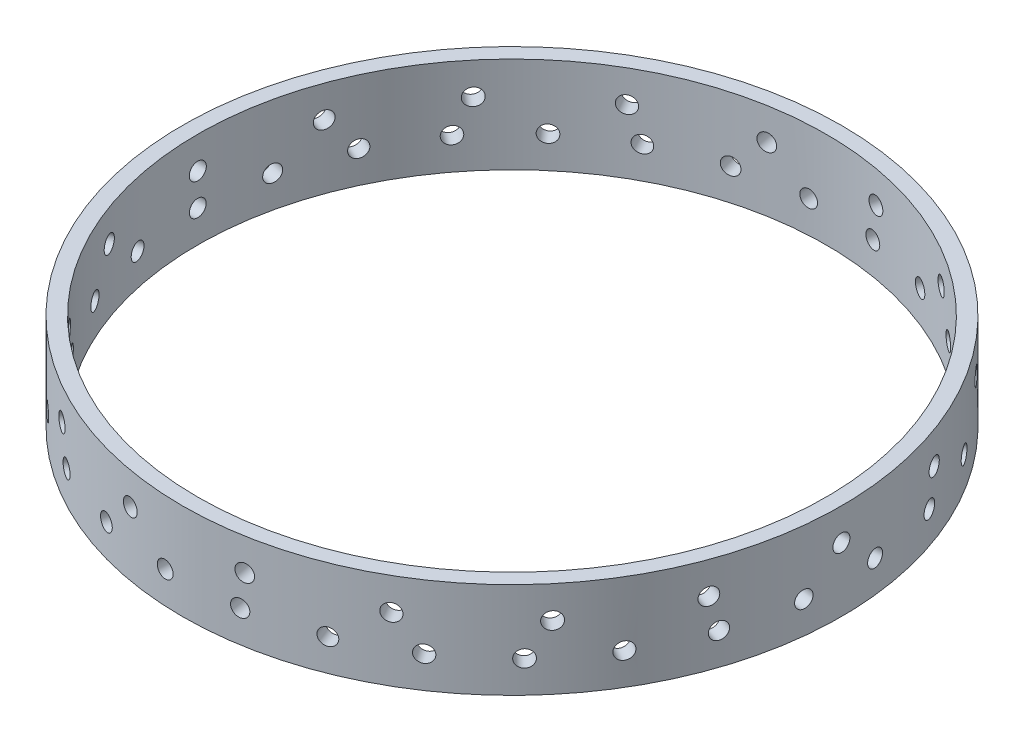
SolidWorks part; units mm, degrees
ref_plane "Front Plane" through (0, 0, 0) normal (0, 0, 1) x (1, 0, 0)
ref_plane "Top Plane" through (0, 0, 0) normal (0, 1, 0) x (1, 0, 0)
ref_plane "Right Plane" through (0, 0, 0) normal (1, 0, 0) x (0, 0, -1)
sketch "Sketch3" plane through (0, 0, 0) normal (1, 0, 0) x (0, 0, -1)
  line L0 (0, 0) -> (0, 34.4201) construction
  point P3 (0, 34.4201)
sketch "Sketch1" plane through (0, 0, 0) normal (0, 1, 0) x (1, 0, 0)
  circle A0 centre (0, 0) radius 68.58
  circle A1 centre (0, 0) radius 65.405
  dimension "D1" = 130.81
  dimension "D2" = 137.16
extrude "Boss-Extrude1" add sketch "Sketch1" along normal blind 19.9644
sketch "Sketch2" plane through (0, 0, 0) normal (1, 0, 0) x (0, 0, -1)
  line L0 (-68.58, 0) -> (68.58, 0) construction
  circle A0 centre (0, 6.6548) radius 1.7501
  dimension "D1" = 3.5001
  dimension "D2" = 6.6548
extrude "Cut-Extrude1" cut sketch "Sketch2" against normal blind 81.4324
pattern_circular "CirPattern1" count 29 over 360 about axis through (0, 0, 0) along (0, 1, 0) of "Cut-Extrude1"
sketch "Sketch4" plane through (0, 0, 0) normal (1, 0, 0) x (0, 0, -1)
  line L0 (0, 0) -> (0, 34.4201) construction
  line L1 (65.405, 19.9644) -> (-65.405, 19.9644) construction
  circle A0 centre (0, 13.3181) radius 1.7716
  dimension "D1" = 3.5433
  dimension "D2" = 6.6463
extrude "Cut-Extrude2" cut sketch "Sketch4" against normal blind 81.4324
pattern_circular "CirPattern2" count 18 over 360 about axis through (0, 0, 0) along (0, 1, 0) of "Cut-Extrude2"
